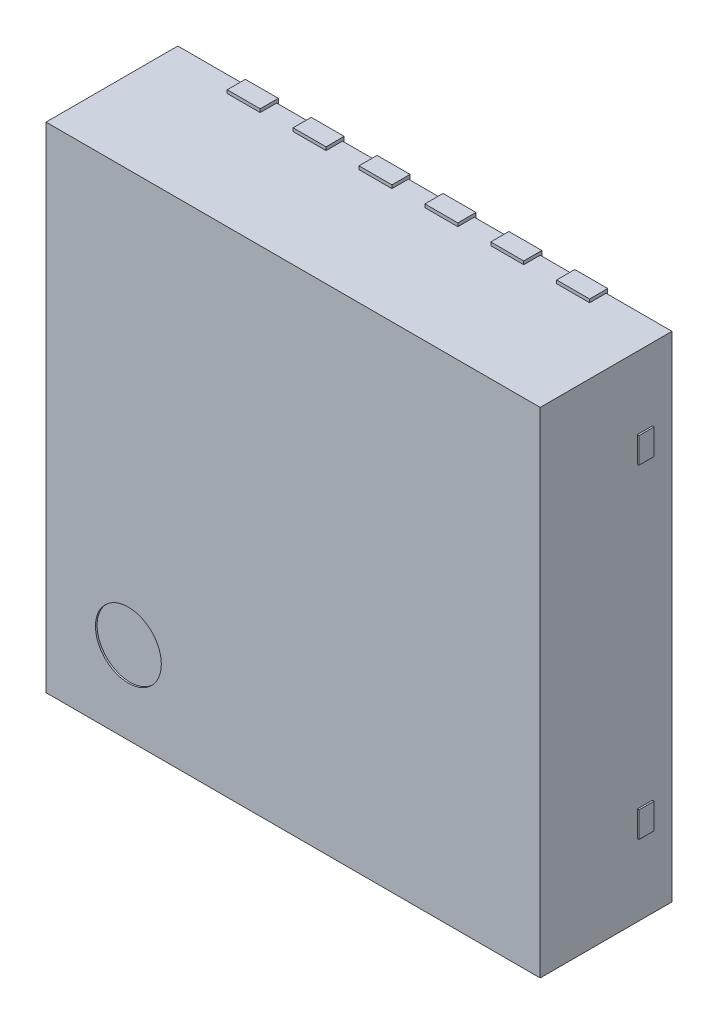
SolidWorks part; units mm, degrees
ref_plane "Front Plane" through (0, 0, 0) normal (0, 0, 1) x (1, 0, 0)
ref_plane "Top Plane" through (0, 0, 0) normal (0, 1, 0) x (1, 0, 0)
ref_plane "Right Plane" through (0, 0, 0) normal (1, 0, 0) x (0, 0, -1)
ref_plane "Plane1" through (0, 0, 0.01) normal (0, 0, 1) x (1, 0, 0)
sketch "Sketch1" plane through (0, 0, 0.01) normal (0, 0, 1) x (1, 0, 0)
  line L1 (-1.5, 1.5) -> (1.5, 1.5)
  line L2 (-1.5, 1.5) -> (-1.5, -1.5)
  line L3 (-1.5, -1.5) -> (1.5, -1.5)
  line L4 (1.5, 1.5) -> (1.5, -1.5)
extrude "Boss-Extrude1" add sketch "Sketch1" along normal blind 0.8
sketch "Sketch2" plane through (0, 0, 0) normal (0, 0, 1) x (1, 0, 0)
  line L1 (-1.1, -1.52) -> (-0.9, -1.52)
  line L2 (-1.1, -1.52) -> (-1.1, -1.1)
  line L3 (-1.1, -1.1) -> (-0.9, -1.1)
  line L4 (-0.9, -1.52) -> (-0.9, -1.1)
  line L5 (-0.7, -1.52) -> (-0.5, -1.52)
  line L6 (-0.7, -1.52) -> (-0.7, -1.1)
  line L7 (-0.7, -1.1) -> (-0.5, -1.1)
  line L8 (-0.5, -1.52) -> (-0.5, -1.1)
  line L9 (-0.3, -1.52) -> (-0.1, -1.52)
  line L10 (-0.3, -1.52) -> (-0.3, -1.1)
  line L11 (-0.3, -1.1) -> (-0.1, -1.1)
  line L12 (-0.1, -1.52) -> (-0.1, -1.1)
  line L13 (0.1, -1.52) -> (0.3, -1.52)
  line L14 (0.1, -1.52) -> (0.1, -1.1)
  line L15 (0.1, -1.1) -> (0.3, -1.1)
  line L16 (0.3, -1.52) -> (0.3, -1.1)
  line L17 (0.5, -1.52) -> (0.7, -1.52)
  line L18 (0.5, -1.52) -> (0.5, -1.1)
  line L19 (0.5, -1.1) -> (0.7, -1.1)
  line L20 (0.7, -1.52) -> (0.7, -1.1)
  line L21 (0.9, -1.52) -> (1.1, -1.52)
  line L22 (0.9, -1.52) -> (0.9, -1.1)
  line L23 (0.9, -1.1) -> (1.1, -1.1)
  line L24 (1.1, -1.52) -> (1.1, -1.1)
  line L25 (-1.6216, 0) -> (1.7822, 0) construction
  line L26 (1.1, 1.52) -> (1.1, 1.1)
  line L27 (0.9, 1.1) -> (1.1, 1.1)
  line L28 (0.9, 1.52) -> (0.9, 1.1)
  line L29 (0.9, 1.52) -> (1.1, 1.52)
  line L30 (0.7, 1.52) -> (0.7, 1.1)
  line L31 (0.5, 1.1) -> (0.7, 1.1)
  line L32 (0.5, 1.52) -> (0.5, 1.1)
  line L33 (0.5, 1.52) -> (0.7, 1.52)
  line L34 (0.3, 1.52) -> (0.3, 1.1)
  line L35 (0.1, 1.1) -> (0.3, 1.1)
  line L36 (0.1, 1.52) -> (0.1, 1.1)
  line L37 (0.1, 1.52) -> (0.3, 1.52)
  line L38 (-0.1, 1.52) -> (-0.1, 1.1)
  line L39 (-0.3, 1.1) -> (-0.1, 1.1)
  line L40 (-0.3, 1.52) -> (-0.3, 1.1)
  line L41 (-0.3, 1.52) -> (-0.1, 1.52)
  line L42 (-0.5, 1.52) -> (-0.5, 1.1)
  line L43 (-0.7, 1.1) -> (-0.5, 1.1)
  line L44 (-0.7, 1.52) -> (-0.7, 1.1)
  line L45 (-0.7, 1.52) -> (-0.5, 1.52)
  line L46 (-0.9, 1.52) -> (-0.9, 1.1)
  line L47 (-1.1, 1.1) -> (-0.9, 1.1)
  line L48 (-1.1, 1.52) -> (-1.1, 1.1)
  line L49 (-1.1, 1.52) -> (-0.9, 1.52)
  line L50 (-1.1, -0.59) -> (-0.85, -0.84)
  line L51 (-1.1, 0.84) -> (1.1, 0.84)
  line L52 (-1.1, 0.84) -> (-1.1, -0.59)
  line L53 (-0.85, -0.84) -> (1.1, -0.84)
  line L54 (1.1, 0.84) -> (1.1, -0.84)
  line L55 (-1.1, -1.52) -> (-0.9, -1.52) [skipped]
  point P55 (-1.1, -0.84)
  dimension "D1" = 6
  dimension "D2" = 0.25
  dimension "D3" = 45
extrude "Boss-Extrude2" add sketch "Sketch2" along normal blind 0.11 separate body
sketch "Sketch3" plane through (1.5, 0, 0) normal (1, 0, 0) x (0, 0, -1)
  line L0 (-0.22, 1.6629) -> (-0.22, -1.6216) construction
  line L2 (0, 0) -> (-0.9261, 0) construction
  line L3 (-0.22, 1.062) -> (-0.1279, 1.062)
  line L4 (-0.22, 1.062) -> (-0.22, 0.906)
  line L5 (-0.22, 0.906) -> (-0.1279, 0.906)
  line L6 (-0.1279, 1.062) -> (-0.1279, 0.906)
  line L7 (-0.1279, -1.062) -> (-0.1279, -0.906)
  line L8 (-0.22, -0.906) -> (-0.1279, -0.906)
  line L9 (-0.22, -1.062) -> (-0.22, -0.906)
  line L10 (-0.22, -1.062) -> (-0.1279, -1.062)
extrude "Boss-Extrude3" add sketch "Sketch3" along normal blind 0.01 separate body
mirror "Mirror1" about plane through (0, 0, 0) normal (1, 0, 0) of "Boss-Extrude3"
sketch "Sketch4" plane through (0, 0, 0.81) normal (0, 0, 1) x (1, 0, 0)
  circle A0 centre (-1, -1) radius 0.2
extrude "Cut-Extrude1" cut sketch "Sketch4" against normal blind 0.01
